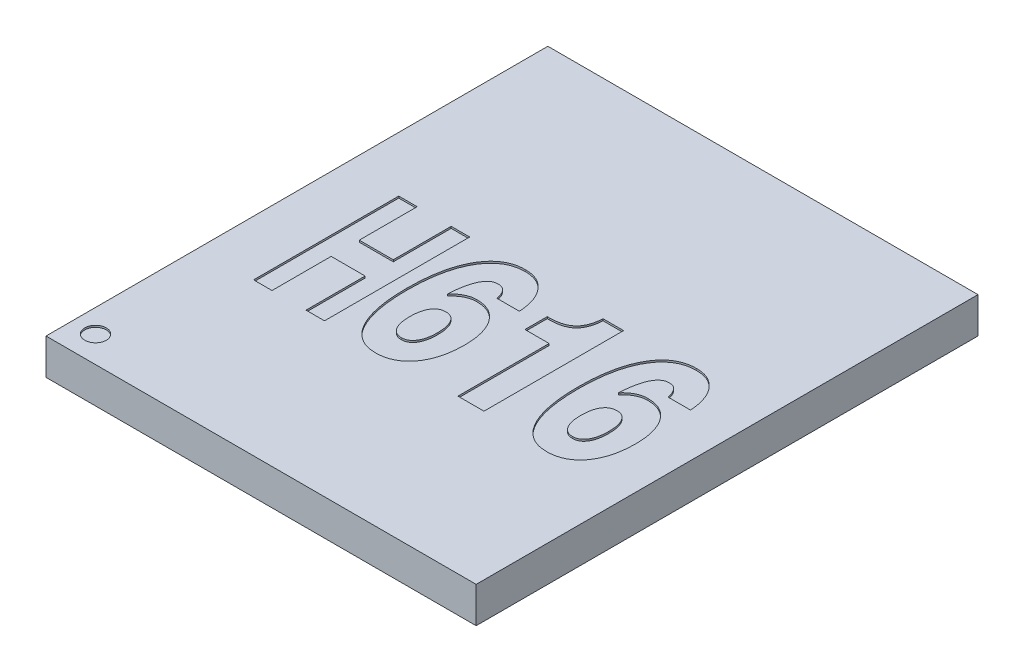
SolidWorks part; units mm, degrees
ref_plane "Front Plane" through (0, 0, 0) normal (0, 0, 1) x (1, 0, 0)
ref_plane "Top Plane" through (0, 0, 0) normal (0, 1, 0) x (1, 0, 0)
ref_plane "Right Plane" through (0, 0, 0) normal (1, 0, 0) x (0, 0, -1)
sketch "Sketch1" plane through (0, 0, 0) normal (0, 1, 0) x (1, 0, 0)
  line L1 (6, -7) -> (-6, -7)
  line L2 (6, -7) -> (6, 7)
  line L3 (6, 7) -> (-6, 7)
  line L4 (-6, -7) -> (-6, 7)
  line L5 (6, -7) -> (-6, 7) construction
  line L6 (6, 7) -> (-6, -7) construction
  point P0 (0, 0)
extrude "Boss-Extrude1" add sketch "Sketch1" along normal blind 1
sketch "Sketch2" plane through (0, 0, 0) normal (0, -1, 0) x (1, 0, 0)
  circle A0 centre (5.5, -6.525) radius 0.175
  circle A1 centre (-5.5, -6.525) radius 0.175
  circle A2 centre (4.85, -6.525) radius 0.175
  circle A3 centre (4.2, -6.525) radius 0.175
  circle A4 centre (3.55, -6.525) radius 0.175
  circle A5 centre (2.9, -6.525) radius 0.175
  circle A6 centre (2.25, -6.525) radius 0.175
  circle A7 centre (1.6, -6.525) radius 0.175
  circle A8 centre (0.95, -6.525) radius 0.175
  circle A9 centre (0.3, -6.525) radius 0.175
  circle A10 centre (-0.35, -6.525) radius 0.175
  circle A11 centre (-1, -6.525) radius 0.175
  circle A12 centre (-1.65, -6.525) radius 0.175
  circle A13 centre (-2.3, -6.525) radius 0.175
  circle A14 centre (-2.95, -6.525) radius 0.175
  circle A15 centre (-3.6, -6.525) radius 0.175
  circle A16 centre (-4.25, -6.525) radius 0.175
  circle A17 centre (-4.9, -6.525) radius 0.175
  circle A19 centre (4.85, -5.875) radius 0.175
  circle A20 centre (4.2, -5.875) radius 0.175
  circle A21 centre (3.55, -5.875) radius 0.175
  circle A22 centre (2.9, -5.875) radius 0.175
  circle A23 centre (2.25, -5.875) radius 0.175
  circle A24 centre (1.6, -5.875) radius 0.175
  circle A25 centre (0.95, -5.875) radius 0.175
  circle A26 centre (0.3, -5.875) radius 0.175
  circle A27 centre (-0.35, -5.875) radius 0.175
  circle A28 centre (-1, -5.875) radius 0.175
  circle A29 centre (-1.65, -5.875) radius 0.175
  circle A30 centre (-2.3, -5.875) radius 0.175
  circle A31 centre (-2.95, -5.875) radius 0.175
  circle A32 centre (-3.6, -5.875) radius 0.175
  circle A33 centre (-4.25, -5.875) radius 0.175
  circle A34 centre (-4.9, -5.875) radius 0.175
  circle A35 centre (-5.55, -5.875) radius 0.175
  circle A36 centre (4.85, -5.225) radius 0.175
  circle A51 centre (-4.9, -5.225) radius 0.175
  circle A52 centre (-5.55, -5.225) radius 0.175
  circle A53 centre (4.85, -4.575) radius 0.175
  circle A68 centre (-4.9, -4.575) radius 0.175
  circle A69 centre (-5.55, -4.575) radius 0.175
  circle A70 centre (4.85, -3.925) radius 0.175
  circle A85 centre (-4.9, -3.925) radius 0.175
  circle A86 centre (-5.55, -3.925) radius 0.175
  circle A87 centre (4.85, -3.275) radius 0.175
  circle A102 centre (-4.9, -3.275) radius 0.175
  circle A103 centre (-5.55, -3.275) radius 0.175
  circle A104 centre (4.85, -2.625) radius 0.175
  circle A119 centre (-4.9, -2.625) radius 0.175
  circle A120 centre (-5.55, -2.625) radius 0.175
  circle A121 centre (4.85, -1.975) radius 0.175
  circle A136 centre (-4.9, -1.975) radius 0.175
  circle A137 centre (-5.55, -1.975) radius 0.175
  circle A138 centre (4.85, -1.325) radius 0.175
  circle A153 centre (-4.9, -1.325) radius 0.175
  circle A154 centre (-5.55, -1.325) radius 0.175
  circle A155 centre (4.85, -0.675) radius 0.175
  circle A170 centre (-4.9, -0.675) radius 0.175
  circle A171 centre (-5.55, -0.675) radius 0.175
  circle A172 centre (4.85, -0.025) radius 0.175
  circle A187 centre (-4.9, -0.025) radius 0.175
  circle A188 centre (-5.55, -0.025) radius 0.175
  circle A189 centre (4.85, 0.625) radius 0.175
  circle A204 centre (-4.9, 0.625) radius 0.175
  circle A205 centre (-5.55, 0.625) radius 0.175
  circle A206 centre (4.85, 1.275) radius 0.175
  circle A221 centre (-4.9, 1.275) radius 0.175
  circle A222 centre (-5.55, 1.275) radius 0.175
  circle A223 centre (4.85, 1.925) radius 0.175
  circle A238 centre (-4.9, 1.925) radius 0.175
  circle A239 centre (-5.55, 1.925) radius 0.175
  circle A240 centre (4.85, 2.575) radius 0.175
  circle A255 centre (-4.9, 2.575) radius 0.175
  circle A256 centre (-5.55, 2.575) radius 0.175
  circle A257 centre (4.85, 3.225) radius 0.175
  circle A272 centre (-4.9, 3.225) radius 0.175
  circle A273 centre (-5.55, 3.225) radius 0.175
  circle A274 centre (4.85, 3.875) radius 0.175
  circle A289 centre (-4.9, 3.875) radius 0.175
  circle A290 centre (-5.55, 3.875) radius 0.175
  circle A291 centre (4.85, 4.525) radius 0.175
  circle A306 centre (-4.9, 4.525) radius 0.175
  circle A307 centre (-5.55, 4.525) radius 0.175
  circle A308 centre (4.85, 5.175) radius 0.175
  circle A323 centre (-4.9, 5.175) radius 0.175
  circle A324 centre (-5.55, 5.175) radius 0.175
  circle A325 centre (4.85, 5.825) radius 0.175
  circle A326 centre (4.2, 5.825) radius 0.175
  circle A327 centre (3.55, 5.825) radius 0.175
  circle A328 centre (2.9, 5.825) radius 0.175
  circle A329 centre (2.25, 5.825) radius 0.175
  circle A330 centre (1.6, 5.825) radius 0.175
  circle A331 centre (0.95, 5.825) radius 0.175
  circle A332 centre (0.3, 5.825) radius 0.175
  circle A333 centre (-0.35, 5.825) radius 0.175
  circle A334 centre (-1, 5.825) radius 0.175
  circle A335 centre (-1.65, 5.825) radius 0.175
  circle A336 centre (-2.3, 5.825) radius 0.175
  circle A337 centre (-2.95, 5.825) radius 0.175
  circle A338 centre (-3.6, 5.825) radius 0.175
  circle A339 centre (-4.25, 5.825) radius 0.175
  circle A340 centre (-4.9, 5.825) radius 0.175
  circle A341 centre (-5.55, 5.825) radius 0.175
  circle A342 centre (4.85, 6.475) radius 0.175
  circle A343 centre (4.2, 6.475) radius 0.175
  circle A344 centre (3.55, 6.475) radius 0.175
  circle A345 centre (2.9, 6.475) radius 0.175
  circle A346 centre (2.25, 6.475) radius 0.175
  circle A347 centre (1.6, 6.475) radius 0.175
  circle A348 centre (0.95, 6.475) radius 0.175
  circle A349 centre (0.3, 6.475) radius 0.175
  circle A350 centre (-0.35, 6.475) radius 0.175
  circle A351 centre (-1, 6.475) radius 0.175
  circle A352 centre (-1.65, 6.475) radius 0.175
  circle A353 centre (-2.3, 6.475) radius 0.175
  circle A354 centre (-2.95, 6.475) radius 0.175
  circle A355 centre (-3.6, 6.475) radius 0.175
  circle A356 centre (-4.25, 6.475) radius 0.175
  circle A357 centre (-4.9, 6.475) radius 0.175
  circle A358 centre (-5.55, 6.475) radius 0.175
  circle A359 centre (5.5, -5.875) radius 0.175
  circle A360 centre (5.5, -5.225) radius 0.175
  circle A361 centre (5.5, -4.575) radius 0.175
  circle A362 centre (5.5, -3.925) radius 0.175
  circle A363 centre (5.5, -3.275) radius 0.175
  circle A364 centre (5.5, -2.625) radius 0.175
  circle A365 centre (5.5, -1.975) radius 0.175
  circle A366 centre (5.5, -1.325) radius 0.175
  circle A367 centre (5.5, -0.675) radius 0.175
  circle A368 centre (5.5, -0.025) radius 0.175
  circle A369 centre (5.5, 0.625) radius 0.175
  circle A370 centre (5.5, 1.275) radius 0.175
  circle A371 centre (5.5, 1.925) radius 0.175
  circle A372 centre (5.5, 2.575) radius 0.175
  circle A373 centre (5.5, 3.225) radius 0.175
  circle A374 centre (5.5, 3.875) radius 0.175
  circle A375 centre (5.5, 4.525) radius 0.175
  circle A376 centre (5.5, 5.175) radius 0.175
  circle A377 centre (5.5, 5.825) radius 0.175
  circle A378 centre (5.5, 6.475) radius 0.175
  circle A379 centre (-5.55, -6.525) radius 0.175 [skipped]
  circle A380 centre (4.2, -5.225) radius 0.175 [skipped]
  circle A381 centre (3.55, -5.225) radius 0.175 [skipped]
  circle A382 centre (2.9, -5.225) radius 0.175 [skipped]
  circle A383 centre (2.25, -5.225) radius 0.175 [skipped]
  circle A384 centre (1.6, -5.225) radius 0.175 [skipped]
  circle A385 centre (0.95, -5.225) radius 0.175 [skipped]
  circle A386 centre (0.3, -5.225) radius 0.175 [skipped]
  circle A387 centre (-0.35, -5.225) radius 0.175 [skipped]
  circle A388 centre (-1, -5.225) radius 0.175 [skipped]
  circle A389 centre (-1.65, -5.225) radius 0.175 [skipped]
  circle A390 centre (-2.3, -5.225) radius 0.175 [skipped]
  circle A391 centre (-2.95, -5.225) radius 0.175 [skipped]
  circle A392 centre (-3.6, -5.225) radius 0.175 [skipped]
  circle A393 centre (-4.25, -5.225) radius 0.175 [skipped]
  circle A394 centre (4.2, -4.575) radius 0.175 [skipped]
  circle A395 centre (3.55, -4.575) radius 0.175 [skipped]
  circle A396 centre (2.9, -4.575) radius 0.175 [skipped]
  circle A397 centre (2.25, -4.575) radius 0.175 [skipped]
  circle A398 centre (1.6, -4.575) radius 0.175 [skipped]
  circle A399 centre (0.95, -4.575) radius 0.175 [skipped]
  circle A400 centre (0.3, -4.575) radius 0.175 [skipped]
  circle A401 centre (-0.35, -4.575) radius 0.175 [skipped]
  circle A402 centre (-1, -4.575) radius 0.175 [skipped]
  circle A403 centre (-1.65, -4.575) radius 0.175 [skipped]
  circle A404 centre (-2.3, -4.575) radius 0.175 [skipped]
  circle A405 centre (-2.95, -4.575) radius 0.175 [skipped]
  circle A406 centre (-3.6, -4.575) radius 0.175 [skipped]
  circle A407 centre (-4.25, -4.575) radius 0.175 [skipped]
  circle A408 centre (4.2, -3.925) radius 0.175 [skipped]
  circle A409 centre (3.55, -3.925) radius 0.175 [skipped]
  circle A410 centre (2.9, -3.925) radius 0.175 [skipped]
  circle A411 centre (2.25, -3.925) radius 0.175 [skipped]
  circle A412 centre (1.6, -3.925) radius 0.175 [skipped]
  circle A413 centre (0.95, -3.925) radius 0.175 [skipped]
  circle A414 centre (0.3, -3.925) radius 0.175 [skipped]
  circle A415 centre (-0.35, -3.925) radius 0.175 [skipped]
  circle A416 centre (-1, -3.925) radius 0.175 [skipped]
  circle A417 centre (-1.65, -3.925) radius 0.175 [skipped]
  circle A418 centre (-2.3, -3.925) radius 0.175 [skipped]
  circle A419 centre (-2.95, -3.925) radius 0.175 [skipped]
  circle A420 centre (-3.6, -3.925) radius 0.175 [skipped]
  circle A421 centre (-4.25, -3.925) radius 0.175 [skipped]
  circle A422 centre (4.2, -3.275) radius 0.175 [skipped]
  circle A423 centre (3.55, -3.275) radius 0.175 [skipped]
  circle A424 centre (2.9, -3.275) radius 0.175 [skipped]
  circle A425 centre (2.25, -3.275) radius 0.175 [skipped]
  circle A426 centre (1.6, -3.275) radius 0.175 [skipped]
  circle A427 centre (0.95, -3.275) radius 0.175 [skipped]
  circle A428 centre (0.3, -3.275) radius 0.175 [skipped]
  circle A429 centre (-0.35, -3.275) radius 0.175 [skipped]
  circle A430 centre (-1, -3.275) radius 0.175 [skipped]
  circle A431 centre (-1.65, -3.275) radius 0.175 [skipped]
  circle A432 centre (-2.3, -3.275) radius 0.175 [skipped]
  circle A433 centre (-2.95, -3.275) radius 0.175 [skipped]
  circle A434 centre (-3.6, -3.275) radius 0.175 [skipped]
  circle A435 centre (-4.25, -3.275) radius 0.175 [skipped]
  circle A436 centre (4.2, -2.625) radius 0.175 [skipped]
  circle A437 centre (3.55, -2.625) radius 0.175 [skipped]
  circle A438 centre (2.9, -2.625) radius 0.175 [skipped]
  circle A439 centre (2.25, -2.625) radius 0.175 [skipped]
  circle A440 centre (1.6, -2.625) radius 0.175 [skipped]
  circle A441 centre (0.95, -2.625) radius 0.175 [skipped]
  circle A442 centre (0.3, -2.625) radius 0.175 [skipped]
  circle A443 centre (-0.35, -2.625) radius 0.175 [skipped]
  circle A444 centre (-1, -2.625) radius 0.175 [skipped]
  circle A445 centre (-1.65, -2.625) radius 0.175 [skipped]
  circle A446 centre (-2.3, -2.625) radius 0.175 [skipped]
  circle A447 centre (-2.95, -2.625) radius 0.175 [skipped]
  circle A448 centre (-3.6, -2.625) radius 0.175 [skipped]
  circle A449 centre (-4.25, -2.625) radius 0.175 [skipped]
  circle A450 centre (4.2, -1.975) radius 0.175 [skipped]
  circle A451 centre (3.55, -1.975) radius 0.175 [skipped]
  circle A452 centre (2.9, -1.975) radius 0.175 [skipped]
  circle A453 centre (2.25, -1.975) radius 0.175 [skipped]
  circle A454 centre (1.6, -1.975) radius 0.175 [skipped]
  circle A455 centre (0.95, -1.975) radius 0.175 [skipped]
  circle A456 centre (0.3, -1.975) radius 0.175 [skipped]
  circle A457 centre (-0.35, -1.975) radius 0.175 [skipped]
  circle A458 centre (-1, -1.975) radius 0.175 [skipped]
  circle A459 centre (-1.65, -1.975) radius 0.175 [skipped]
  circle A460 centre (-2.3, -1.975) radius 0.175 [skipped]
  circle A461 centre (-2.95, -1.975) radius 0.175 [skipped]
  circle A462 centre (-3.6, -1.975) radius 0.175 [skipped]
  circle A463 centre (-4.25, -1.975) radius 0.175 [skipped]
  circle A464 centre (4.2, -1.325) radius 0.175 [skipped]
  circle A465 centre (3.55, -1.325) radius 0.175 [skipped]
  circle A466 centre (2.9, -1.325) radius 0.175 [skipped]
  circle A467 centre (2.25, -1.325) radius 0.175 [skipped]
  circle A468 centre (1.6, -1.325) radius 0.175 [skipped]
  circle A469 centre (0.95, -1.325) radius 0.175 [skipped]
  circle A470 centre (0.3, -1.325) radius 0.175 [skipped]
  circle A471 centre (-0.35, -1.325) radius 0.175 [skipped]
  circle A472 centre (-1, -1.325) radius 0.175 [skipped]
  circle A473 centre (-1.65, -1.325) radius 0.175 [skipped]
  circle A474 centre (-2.3, -1.325) radius 0.175 [skipped]
  circle A475 centre (-2.95, -1.325) radius 0.175 [skipped]
  circle A476 centre (-3.6, -1.325) radius 0.175 [skipped]
  circle A477 centre (-4.25, -1.325) radius 0.175 [skipped]
  circle A478 centre (4.2, -0.675) radius 0.175 [skipped]
  circle A479 centre (3.55, -0.675) radius 0.175 [skipped]
  circle A480 centre (2.9, -0.675) radius 0.175 [skipped]
  circle A481 centre (2.25, -0.675) radius 0.175 [skipped]
  circle A482 centre (1.6, -0.675) radius 0.175 [skipped]
  circle A483 centre (0.95, -0.675) radius 0.175 [skipped]
  circle A484 centre (0.3, -0.675) radius 0.175 [skipped]
  circle A485 centre (-0.35, -0.675) radius 0.175 [skipped]
  circle A486 centre (-1, -0.675) radius 0.175 [skipped]
  circle A487 centre (-1.65, -0.675) radius 0.175 [skipped]
  circle A488 centre (-2.3, -0.675) radius 0.175 [skipped]
  circle A489 centre (-2.95, -0.675) radius 0.175 [skipped]
  circle A490 centre (-3.6, -0.675) radius 0.175 [skipped]
  circle A491 centre (-4.25, -0.675) radius 0.175 [skipped]
  circle A492 centre (4.2, -0.025) radius 0.175 [skipped]
  circle A493 centre (3.55, -0.025) radius 0.175 [skipped]
  circle A494 centre (2.9, -0.025) radius 0.175 [skipped]
  circle A495 centre (2.25, -0.025) radius 0.175 [skipped]
  circle A496 centre (1.6, -0.025) radius 0.175 [skipped]
  circle A497 centre (0.95, -0.025) radius 0.175 [skipped]
  circle A498 centre (0.3, -0.025) radius 0.175 [skipped]
  circle A499 centre (-0.35, -0.025) radius 0.175 [skipped]
  circle A500 centre (-1, -0.025) radius 0.175 [skipped]
  circle A501 centre (-1.65, -0.025) radius 0.175 [skipped]
  circle A502 centre (-2.3, -0.025) radius 0.175 [skipped]
  circle A503 centre (-2.95, -0.025) radius 0.175 [skipped]
  circle A504 centre (-3.6, -0.025) radius 0.175 [skipped]
  circle A505 centre (-4.25, -0.025) radius 0.175 [skipped]
  circle A506 centre (4.2, 0.625) radius 0.175 [skipped]
  circle A507 centre (3.55, 0.625) radius 0.175 [skipped]
  circle A508 centre (2.9, 0.625) radius 0.175 [skipped]
  circle A509 centre (2.25, 0.625) radius 0.175 [skipped]
  circle A510 centre (1.6, 0.625) radius 0.175 [skipped]
  circle A511 centre (0.95, 0.625) radius 0.175 [skipped]
  circle A512 centre (0.3, 0.625) radius 0.175 [skipped]
  circle A513 centre (-0.35, 0.625) radius 0.175 [skipped]
  circle A514 centre (-1, 0.625) radius 0.175 [skipped]
  circle A515 centre (-1.65, 0.625) radius 0.175 [skipped]
  circle A516 centre (-2.3, 0.625) radius 0.175 [skipped]
  circle A517 centre (-2.95, 0.625) radius 0.175 [skipped]
  circle A518 centre (-3.6, 0.625) radius 0.175 [skipped]
  circle A519 centre (-4.25, 0.625) radius 0.175 [skipped]
  circle A520 centre (4.2, 1.275) radius 0.175 [skipped]
  circle A521 centre (3.55, 1.275) radius 0.175 [skipped]
  circle A522 centre (2.9, 1.275) radius 0.175 [skipped]
  circle A523 centre (2.25, 1.275) radius 0.175 [skipped]
  circle A524 centre (1.6, 1.275) radius 0.175 [skipped]
  circle A525 centre (0.95, 1.275) radius 0.175 [skipped]
  circle A526 centre (0.3, 1.275) radius 0.175 [skipped]
  circle A527 centre (-0.35, 1.275) radius 0.175 [skipped]
  circle A528 centre (-1, 1.275) radius 0.175 [skipped]
  circle A529 centre (-1.65, 1.275) radius 0.175 [skipped]
  circle A530 centre (-2.3, 1.275) radius 0.175 [skipped]
  circle A531 centre (-2.95, 1.275) radius 0.175 [skipped]
  circle A532 centre (-3.6, 1.275) radius 0.175 [skipped]
  circle A533 centre (-4.25, 1.275) radius 0.175 [skipped]
  circle A534 centre (4.2, 1.925) radius 0.175 [skipped]
  circle A535 centre (3.55, 1.925) radius 0.175 [skipped]
  circle A536 centre (2.9, 1.925) radius 0.175 [skipped]
  circle A537 centre (2.25, 1.925) radius 0.175 [skipped]
  circle A538 centre (1.6, 1.925) radius 0.175 [skipped]
  circle A539 centre (0.95, 1.925) radius 0.175 [skipped]
  circle A540 centre (0.3, 1.925) radius 0.175 [skipped]
  circle A541 centre (-0.35, 1.925) radius 0.175 [skipped]
  circle A542 centre (-1, 1.925) radius 0.175 [skipped]
  circle A543 centre (-1.65, 1.925) radius 0.175 [skipped]
  circle A544 centre (-2.3, 1.925) radius 0.175 [skipped]
  circle A545 centre (-2.95, 1.925) radius 0.175 [skipped]
  circle A546 centre (-3.6, 1.925) radius 0.175 [skipped]
  circle A547 centre (-4.25, 1.925) radius 0.175 [skipped]
  circle A548 centre (4.2, 2.575) radius 0.175 [skipped]
  circle A549 centre (3.55, 2.575) radius 0.175 [skipped]
  circle A550 centre (2.9, 2.575) radius 0.175 [skipped]
  circle A551 centre (2.25, 2.575) radius 0.175 [skipped]
  circle A552 centre (1.6, 2.575) radius 0.175 [skipped]
  circle A553 centre (0.95, 2.575) radius 0.175 [skipped]
  circle A554 centre (0.3, 2.575) radius 0.175 [skipped]
  circle A555 centre (-0.35, 2.575) radius 0.175 [skipped]
  circle A556 centre (-1, 2.575) radius 0.175 [skipped]
  circle A557 centre (-1.65, 2.575) radius 0.175 [skipped]
  circle A558 centre (-2.3, 2.575) radius 0.175 [skipped]
  circle A559 centre (-2.95, 2.575) radius 0.175 [skipped]
  circle A560 centre (-3.6, 2.575) radius 0.175 [skipped]
  circle A561 centre (-4.25, 2.575) radius 0.175 [skipped]
  circle A562 centre (4.2, 3.225) radius 0.175 [skipped]
  circle A563 centre (3.55, 3.225) radius 0.175 [skipped]
  circle A564 centre (2.9, 3.225) radius 0.175 [skipped]
  circle A565 centre (2.25, 3.225) radius 0.175 [skipped]
  circle A566 centre (1.6, 3.225) radius 0.175 [skipped]
  circle A567 centre (0.95, 3.225) radius 0.175 [skipped]
  circle A568 centre (0.3, 3.225) radius 0.175 [skipped]
  circle A569 centre (-0.35, 3.225) radius 0.175 [skipped]
  circle A570 centre (-1, 3.225) radius 0.175 [skipped]
  circle A571 centre (-1.65, 3.225) radius 0.175 [skipped]
  circle A572 centre (-2.3, 3.225) radius 0.175 [skipped]
  circle A573 centre (-2.95, 3.225) radius 0.175 [skipped]
  circle A574 centre (-3.6, 3.225) radius 0.175 [skipped]
  circle A575 centre (-4.25, 3.225) radius 0.175 [skipped]
  circle A576 centre (4.2, 3.875) radius 0.175 [skipped]
  circle A577 centre (3.55, 3.875) radius 0.175 [skipped]
  circle A578 centre (2.9, 3.875) radius 0.175 [skipped]
  circle A579 centre (2.25, 3.875) radius 0.175 [skipped]
  circle A580 centre (1.6, 3.875) radius 0.175 [skipped]
  circle A581 centre (0.95, 3.875) radius 0.175 [skipped]
  circle A582 centre (0.3, 3.875) radius 0.175 [skipped]
  circle A583 centre (-0.35, 3.875) radius 0.175 [skipped]
  circle A584 centre (-1, 3.875) radius 0.175 [skipped]
  circle A585 centre (-1.65, 3.875) radius 0.175 [skipped]
  circle A586 centre (-2.3, 3.875) radius 0.175 [skipped]
  circle A587 centre (-2.95, 3.875) radius 0.175 [skipped]
  circle A588 centre (-3.6, 3.875) radius 0.175 [skipped]
  circle A589 centre (-4.25, 3.875) radius 0.175 [skipped]
  circle A590 centre (4.2, 4.525) radius 0.175 [skipped]
  circle A591 centre (3.55, 4.525) radius 0.175 [skipped]
  circle A592 centre (2.9, 4.525) radius 0.175 [skipped]
  circle A593 centre (2.25, 4.525) radius 0.175 [skipped]
  circle A594 centre (1.6, 4.525) radius 0.175 [skipped]
  circle A595 centre (0.95, 4.525) radius 0.175 [skipped]
  circle A596 centre (0.3, 4.525) radius 0.175 [skipped]
  circle A597 centre (-0.35, 4.525) radius 0.175 [skipped]
  circle A598 centre (-1, 4.525) radius 0.175 [skipped]
  circle A599 centre (-1.65, 4.525) radius 0.175 [skipped]
  circle A600 centre (-2.3, 4.525) radius 0.175 [skipped]
  circle A601 centre (-2.95, 4.525) radius 0.175 [skipped]
  circle A602 centre (-3.6, 4.525) radius 0.175 [skipped]
  circle A603 centre (-4.25, 4.525) radius 0.175 [skipped]
  circle A604 centre (4.2, 5.175) radius 0.175 [skipped]
  circle A605 centre (3.55, 5.175) radius 0.175 [skipped]
  circle A606 centre (2.9, 5.175) radius 0.175 [skipped]
  circle A607 centre (2.25, 5.175) radius 0.175 [skipped]
  circle A608 centre (1.6, 5.175) radius 0.175 [skipped]
  circle A609 centre (0.95, 5.175) radius 0.175 [skipped]
  circle A610 centre (0.3, 5.175) radius 0.175 [skipped]
  circle A611 centre (-0.35, 5.175) radius 0.175 [skipped]
  circle A612 centre (-1, 5.175) radius 0.175 [skipped]
  circle A613 centre (-1.65, 5.175) radius 0.175 [skipped]
  circle A614 centre (-2.3, 5.175) radius 0.175 [skipped]
  circle A615 centre (-2.95, 5.175) radius 0.175 [skipped]
  circle A616 centre (-3.6, 5.175) radius 0.175 [skipped]
  circle A617 centre (-4.25, 5.175) radius 0.175 [skipped]
  dimension "D1" = 18
  dimension "D2" = 21
extrude "Boss-Extrude2" add sketch "Sketch2" along normal blind 0.12
fillet "Fillet2" radius 0.08 130 edges at (5.5, -0.12, 6.3) (5.5, -0.12, 5.65) (5.5, -0.12, 5) (5.5, -0.12, 4.35) (5.5, -0.12, 3.7) (5.5, -0.12, 3.05) (5.5, -0.12, 2.4) (5.5, -0.12, 1.75) (5.5, -0.12, 1.1) (5.5, -0.12, 0.45) (5.5, -0.12, -0.2) (5.5, -0.12, -2.15) (5.5, -0.12, -2.8) (5.5, -0.12, -3.45) (5.5, -0.12, -4.1) (5.5, -0.12, -4.75) (5.5, -0.12, -5.4) (5.5, -0.12, -6.05) (-5.55, -0.12, 6.3) (-4.9, -0.12, 6.3) (-4.25, -0.12, 6.3) (-3.6, -0.12, 6.3) (-2.95, -0.12, 6.3) (-2.3, -0.12, 6.3) (-1.65, -0.12, 6.3) (-1, -0.12, 6.3) (-0.35, -0.12, 6.3) (0.3, -0.12, 6.3) (0.95, -0.12, 6.3) (1.6, -0.12, 6.3) (2.25, -0.12, 6.3) (2.9, -0.12, 6.3) (3.55, -0.12, 6.3) (4.2, -0.12, 6.3) (4.85, -0.12, 6.3) (-5.55, -0.12, 5.65) (-4.9, -0.12, 5.65) (-4.25, -0.12, 5.65) (-3.6, -0.12, 5.65) (-2.95, -0.12, 5.65) (-2.3, -0.12, 5.65) (-1.65, -0.12, 5.65) (-1, -0.12, 5.65) (0.3, -0.12, 5.65) (0.95, -0.12, 5.65) (1.6, -0.12, 5.65) (2.25, -0.12, 5.65) (3.55, -0.12, 5.65) (4.2, -0.12, 5.65) (4.85, -0.12, 5.65) (-4.9, -0.12, 5) (4.85, -0.12, 5) (-5.55, -0.12, 4.35) (-4.9, -0.12, 4.35) (4.85, -0.12, 4.35) (-5.55, -0.12, 3.7) (-4.9, -0.12, 3.05) (4.85, -0.12, 3.05) (-5.55, -0.12, 2.4) (-4.9, -0.12, 2.4) (4.85, -0.12, 2.4) (-5.55, -0.12, 1.75) (-4.9, -0.12, 1.75) (4.85, -0.12, 1.75) (-4.9, -0.12, 1.1) (4.85, -0.12, 1.1) (-5.55, -0.12, 0.45) (-4.9, -0.12, 0.45) (4.85, -0.12, 0.45) (-5.55, -0.12, -0.2) (-4.9, -0.12, -0.2) (4.85, -0.12, -0.2) (-5.55, -0.12, -0.85) (-4.9, -0.12, -0.85) (4.85, -0.12, -0.85) (-5.55, -0.12, -1.5) (-4.9, -0.12, -1.5) (4.85, -0.12, -1.5) (-5.55, -0.12, -2.15) (-4.9, -0.12, -2.15) (4.85, -0.12, -2.15) (-5.55, -0.12, -2.8) (-4.9, -0.12, -2.8) (4.85, -0.12, -2.8) (-5.55, -0.12, -3.45) (-4.9, -0.12, -3.45) (4.85, -0.12, -3.45) (-5.55, -0.12, -4.1) (-4.9, -0.12, -4.1) (4.85, -0.12, -4.1) (-5.55, -0.12, -4.75) (-4.9, -0.12, -4.75) (4.85, -0.12, -4.75) (-5.55, -0.12, -5.4) (-4.9, -0.12, -5.4) (4.85, -0.12, -5.4) (-5.55, -0.12, -6.05) (-4.9, -0.12, -6.05) (-4.25, -0.12, -6.05) (-3.6, -0.12, -6.05) (-2.95, -0.12, -6.05) (-2.3, -0.12, -6.05) (-1.65, -0.12, -6.05) (-1, -0.12, -6.05) (-0.35, -0.12, -6.05) (0.95, -0.12, -6.05) (1.6, -0.12, -6.05) (2.25, -0.12, -6.05) (2.9, -0.12, -6.05) (3.55, -0.12, -6.05) (4.2, -0.12, -6.05) (4.85, -0.12, -6.05) (-4.9, -0.12, -6.7) (-4.25, -0.12, -6.7) (-3.6, -0.12, -6.7) (-2.95, -0.12, -6.7) (-2.3, -0.12, -6.7) (-1.65, -0.12, -6.7) (-1, -0.12, -6.7) (-0.35, -0.12, -6.7) (0.3, -0.12, -6.7) (0.95, -0.12, -6.7) (1.6, -0.12, -6.7) (2.25, -0.12, -6.7) (2.9, -0.12, -6.7) (3.55, -0.12, -6.7) (4.2, -0.12, -6.7) (4.85, -0.12, -6.7) (-5.5, -0.12, -6.7) (5.5, -0.12, -6.7)
sketch "Sketch3" plane through (0, 1, 0) normal (0, 1, 0) x (1, 0, 0)
  line L0 (99.5201, 1303.4564) -> (1099.5201, 1303.4564) construction
  circle A0 centre (-5.3562, -6.262) radius 0.3
  text T0 "<b>H</b>" font "Ebrima" height 4.05
  text T3 "616" font "Swis721 Hv BT" height 4.05
  point P8 (0, 0)
extrude "Cut-Extrude1" cut sketch "Sketch3" against normal blind 0.05
